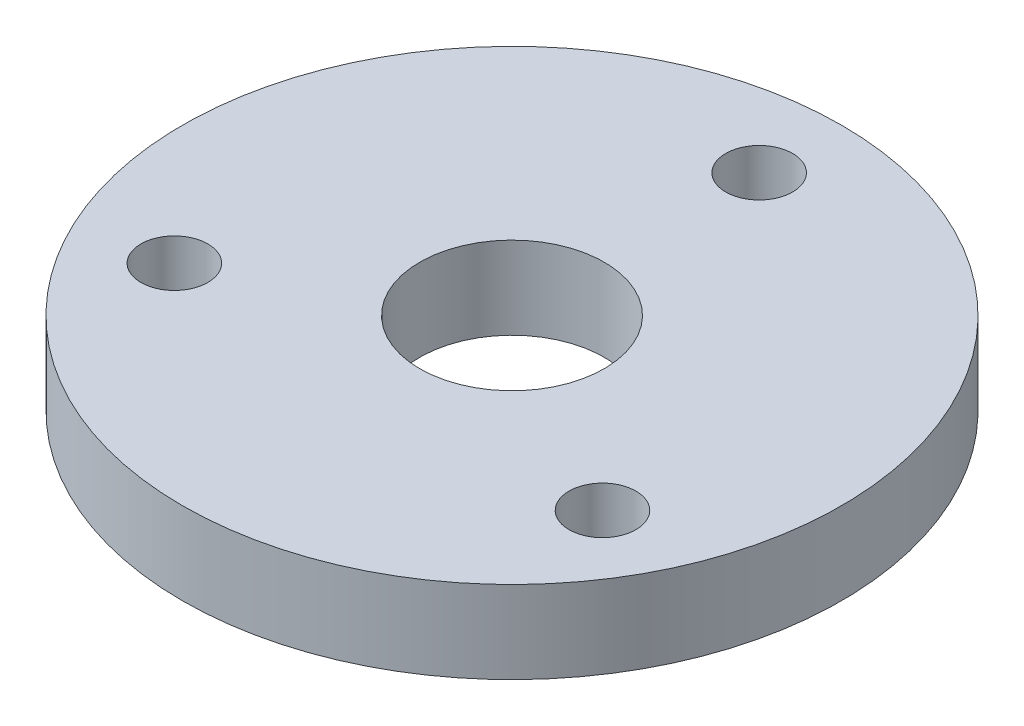
SolidWorks part; units mm, degrees
material "1060 Alloy"
ref_plane "Front Plane" through (0, 0, 0) normal (0, 0, 1) x (1, 0, 0)
ref_plane "Top Plane" through (0, 0, 0) normal (0, 1, 0) x (1, 0, 0)
ref_plane "Right Plane" through (0, 0, 0) normal (1, 0, 0) x (0, 0, -1)
sketch "Sketch1" plane through (0, 0, 0) normal (0, 1, 0) x (1, 0, 0)
  line L0 (0, -161.37) -> (0, 132.9061) construction
  line L1 (-151.3519, 0) -> (186.9249, 0) construction
  line L2 (0, 0) -> (-64.9519, -37.5) construction
  circle A0 centre (0, 0) radius 100
  circle A1 centre (0, 0) radius 28
  circle A2 centre (0, 0) radius 75 construction
  circle A3 centre (0, 75) radius 10.15
  circle A4 centre (64.9519, -37.5) radius 10.15
  circle A5 centre (-64.9519, -37.5) radius 10.15
  point P18 (0, 0)
  dimension "D1" = 200
  dimension "D2" = 56
  dimension "D3" = 150
  dimension "D4" = 20.3
  dimension "D6" = 120
  dimension "D5" = 3
extrude "Boss-Extrude1" add sketch "Sketch1" along normal blind 25
